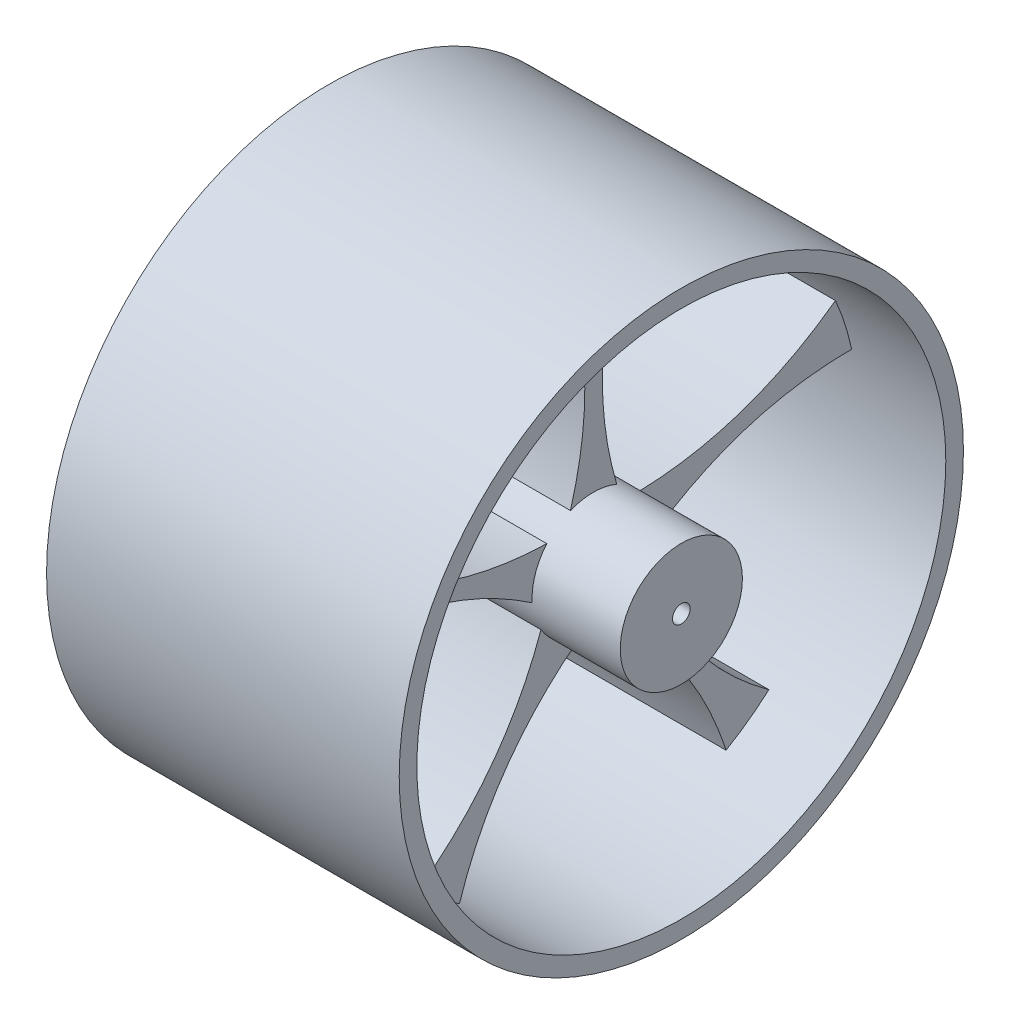
SolidWorks part; units mm, degrees
ref_plane "Front Plane" through (0, 0, 0) normal (0, 0, 1) x (1, 0, 0)
ref_plane "Top Plane" through (0, 0, 0) normal (0, 1, 0) x (1, 0, 0)
ref_plane "Right Plane" through (0, 0, 0) normal (1, 0, 0) x (0, 0, -1)
sketch "Sketch1" plane through (0, 0, 0) normal (1, 0, 0) x (0, 0, -1)
  line L1 (17.3205, 0) -> (8.6603, 15)
  line L2 (8.6603, 15) -> (-8.6603, 15)
  line L3 (-8.6603, 15) -> (-17.3205, 0)
  line L4 (-17.3205, 0) -> (-8.6603, -15)
  line L5 (-8.6603, -15) -> (8.6603, -15)
  line L6 (8.6603, -15) -> (17.3205, 0)
  circle A0 centre (0, 0) radius 15
  circle A1 centre (0, 0) radius 75
  circle A2 centre (0, 0) radius 80
  circle A3 centre (0, 0) radius 15 construction
  circle A4 centre (0, 0) radius 17.3205
  dimension "D1" = 30
  dimension "D2" = 150
  dimension "D4" = 30
  dimension "D3" = 5
extrude "Boss-Extrude1" add sketch "Sketch1" along normal blind 100 contours A2 A1 | A0 | L4 L5 L6 L1 L2 L3 | A4
sketch "Sketch7" plane through (0, 0, 0) normal (-1, 0, 0) x (0, 0, 1)
  line L0 (2.3837, 42.3668) -> (2.3837, 45.4154)
  line L1 (0.1744, -17.3192) -> (15.0861, -8.5085)
  line L2 (15.0861, -8.5085) -> (14.9117, 8.8107)
  line L3 (14.9117, 8.8107) -> (-0.1744, 17.3192)
  line L4 (-0.1744, 17.3192) -> (-15.0861, 8.5085)
  line L5 (-15.0861, 8.5085) -> (-14.9117, -8.8107)
  line L6 (-14.9117, -8.8107) -> (0.1744, -17.3192)
  line L7 (-2.6163, 15.8764) -> (2.3837, 15.8764)
  line L8 (-2.6163, 15.8764) -> (-2.6163, 17.1218)
  line L10 (2.3837, 15.8764) -> (2.3837, 17.1557)
  circle A0 centre (0, 0) radius 17.3205 construction
  circle A1 centre (0, 0) radius 17.3205
  circle A2 centre (0, 0) radius 75 construction
  circle A3 centre (0, 0) radius 75
  circle A4 centre (0, 0) radius 14.9996 construction
  spline S0 degree 2 poles (-7.6303, 12.9139) (2.4251, 43.8479) (-7.6303, 74.6109) knots 0 0 0 1 1 1
  spline S1 degree 2 poles (7.3686, 13.0649) (-2.6257, 43.9314) (7.3686, 74.6371) knots 0 0 0 1 1 1
  circle M13 centre (0, 0) radius 17.3205
  dimension "D1" = 0
  dimension "D2" = 5
extrude "Boss-Extrude2" add sketch "Sketch7" against normal blind 50 from offset 25 contours S1 A3 S0 M13 offset against normal yes
sketch "Sketch5" plane through (100, 0, 0) normal (1, 0, 0) x (0, 0, -1)
  circle A0 centre (0, 0) radius 15
ref_axis "Axis1" through (100, 0, 0) along (-1, 0, 0)
sketch "Sketch6" plane through (0, 0, 0) normal (-1, 0, 0) x (0, 0, 1)
  circle A0 centre (0, 0) radius 2.5
  dimension "D1" = 5
extrude "Cut-Extrude1" cut sketch "Sketch6" against normal blind 100
pattern_circular "CirPattern1" count 5 over 360 about axis through (100, 0, 0) along (-1, 0, 0) of "Boss-Extrude2"
